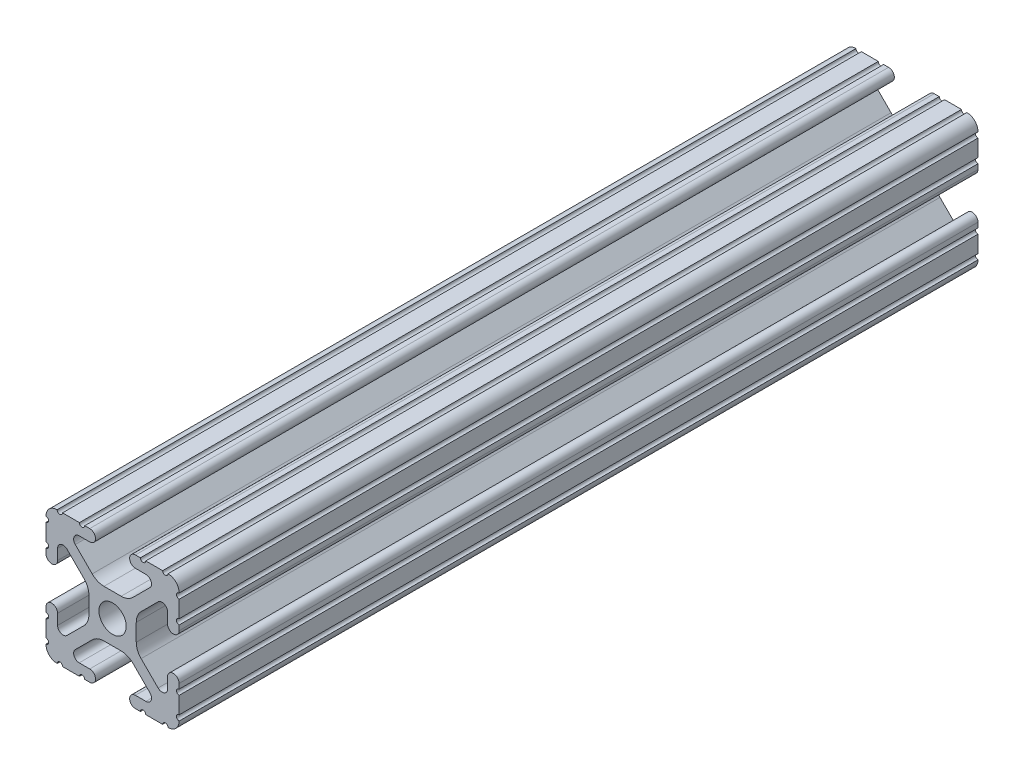
SolidWorks part; units mm, degrees
ref_plane "Front Plane" through (0, 0, 0) normal (0, 0, 1) x (1, 0, 0)
ref_plane "Top Plane" through (0, 0, 0) normal (0, 1, 0) x (1, 0, 0)
ref_plane "Right Plane" through (0, 0, 0) normal (1, 0, 0) x (0, 0, -1)
sketch "Sketch1" plane through (0, 0, 0) normal (1, 0, 0) x (0, 0, -1)
  line L0 (-76.2, 0) -> (76.2, 0)
  point P2 (0, 0)
  dimension "D1" = 152.4
other "Fractional 1010(1)"
ref_plane "Plane1" through (0, 0, 76.2) normal (0, 0, -1) x (0, 1, 0)
sketch "Sketch11" plane through (0, 0, 76.2) normal (0, 0, -1) x (0, 1, 0)
  line L0 (10.5918, 12.7) -> (10.5664, 12.7)
  line L1 (9.5504, 12.7) -> (6.3246, 12.7)
  line L2 (5.3086, 12.7) -> (4.3561, 12.7)
  line L3 (4.3561, 10.4902) -> (6.3701, 10.4902)
  line L4 (7.1192, 8.6817) -> (3.8846, 5.4471)
  line L5 (1.6396, 4.5172) -> (-1.6396, 4.5172)
  line L6 (-3.8846, 5.4471) -> (-7.1192, 8.6817)
  line L7 (-6.3701, 10.4902) -> (-4.3561, 10.4902)
  line L8 (-4.3561, 12.7) -> (-5.3086, 12.7)
  line L9 (-6.3246, 12.7) -> (-9.5504, 12.7)
  line L10 (-10.5664, 12.7) -> (-10.5918, 12.7)
  line L11 (-12.7, 10.5918) -> (-12.7, 10.5664)
  line L12 (-12.7, 9.5504) -> (-12.7, 6.3246)
  line L13 (-12.7, 5.3086) -> (-12.7, 4.3561)
  line L14 (-10.4902, 4.3561) -> (-10.4902, 6.3701)
  line L15 (-8.6817, 7.1192) -> (-5.4471, 3.8846)
  line L16 (-4.5172, 1.6396) -> (-4.5172, -1.6396)
  line L17 (-5.4471, -3.8846) -> (-8.6817, -7.1192)
  line L18 (-10.4902, -6.3701) -> (-10.4902, -4.3561)
  line L19 (-12.7, -4.3561) -> (-12.7, -5.3086)
  line L20 (-12.7, -6.3246) -> (-12.7, -9.5504)
  line L21 (-12.7, -10.5664) -> (-12.7, -10.5918)
  line L22 (-10.5918, -12.7) -> (-10.5664, -12.7)
  line L23 (-9.5504, -12.7) -> (-6.3246, -12.7)
  line L24 (-5.3086, -12.7) -> (-4.3561, -12.7)
  line L25 (-4.3561, -10.4902) -> (-6.3701, -10.4902)
  line L26 (-7.1192, -8.6817) -> (-3.8846, -5.4471)
  line L27 (-1.6396, -4.5172) -> (1.6396, -4.5172)
  line L28 (3.8846, -5.4471) -> (7.1192, -8.6817)
  line L29 (6.3701, -10.4902) -> (4.3561, -10.4902)
  line L30 (4.3561, -12.7) -> (5.3086, -12.7)
  line L31 (6.3246, -12.7) -> (9.5504, -12.7)
  line L32 (10.5664, -12.7) -> (10.5918, -12.7)
  line L33 (12.7, -10.5918) -> (12.7, -10.5664)
  line L34 (12.7, -9.5504) -> (12.7, -6.3246)
  line L35 (12.7, -5.3086) -> (12.7, -4.3561)
  line L36 (10.4902, -4.3561) -> (10.4902, -6.3701)
  line L37 (8.6817, -7.1192) -> (5.4471, -3.8846)
  line L38 (4.5172, -1.6396) -> (4.5172, 1.6396)
  line L39 (5.4471, 3.8846) -> (8.6817, 7.1192)
  line L40 (10.4902, 6.3701) -> (10.4902, 4.3561)
  line L41 (12.7, 4.3561) -> (12.7, 5.3086)
  line L42 (12.7, 6.3246) -> (12.7, 9.5504)
  line L43 (12.7, 10.5664) -> (12.7, 10.5918)
  circle A0 centre (0, 0) radius 2.6035
  arc A1 (12.7, 10.5918) -> (10.5918, 12.7) centre (10.5918, 10.5918) ccw
  arc A2 (9.5504, 12.7) -> (10.5664, 12.7) centre (10.0584, 12.7) ccw
  arc A3 (5.3086, 12.7) -> (6.3246, 12.7) centre (5.8166, 12.7) ccw
  arc A4 (4.3561, 12.7) -> (4.3561, 10.4902) centre (4.3561, 11.5951) ccw
  arc A5 (7.1192, 8.6817) -> (6.3701, 10.4902) centre (6.3701, 9.4308) ccw
  arc A6 (1.6396, 4.5172) -> (3.8846, 5.4471) centre (1.6396, 7.6922) ccw
  arc A7 (-3.8846, 5.4471) -> (-1.6396, 4.5172) centre (-1.6396, 7.6922) ccw
  arc A8 (-6.3701, 10.4902) -> (-7.1192, 8.6817) centre (-6.3701, 9.4308) ccw
  arc A9 (-4.3561, 10.4902) -> (-4.3561, 12.7) centre (-4.3561, 11.5951) ccw
  arc A10 (-6.3246, 12.7) -> (-5.3086, 12.7) centre (-5.8166, 12.7) ccw
  arc A11 (-10.5664, 12.7) -> (-9.5504, 12.7) centre (-10.0584, 12.7) ccw
  arc A12 (-10.5918, 12.7) -> (-12.7, 10.5918) centre (-10.5918, 10.5918) ccw
  arc A13 (-12.7, 9.5504) -> (-12.7, 10.5664) centre (-12.7, 10.0584) ccw
  arc A14 (-12.7, 5.3086) -> (-12.7, 6.3246) centre (-12.7, 5.8166) ccw
  arc A15 (-12.7, 4.3561) -> (-10.4902, 4.3561) centre (-11.5951, 4.3561) ccw
  arc A16 (-8.6817, 7.1192) -> (-10.4902, 6.3701) centre (-9.4308, 6.3701) ccw
  arc A17 (-4.5172, 1.6396) -> (-5.4471, 3.8846) centre (-7.6922, 1.6396) ccw
  arc A18 (-5.4471, -3.8846) -> (-4.5172, -1.6396) centre (-7.6922, -1.6396) ccw
  arc A19 (-10.4902, -6.3701) -> (-8.6817, -7.1192) centre (-9.4308, -6.3701) ccw
  arc A20 (-10.4902, -4.3561) -> (-12.7, -4.3561) centre (-11.5951, -4.3561) ccw
  arc A21 (-12.7, -6.3246) -> (-12.7, -5.3086) centre (-12.7, -5.8166) ccw
  arc A22 (-12.7, -10.5664) -> (-12.7, -9.5504) centre (-12.7, -10.0584) ccw
  arc A23 (-12.7, -10.5918) -> (-10.5918, -12.7) centre (-10.5918, -10.5918) ccw
  arc A24 (-9.5504, -12.7) -> (-10.5664, -12.7) centre (-10.0584, -12.7) ccw
  arc A25 (-5.3086, -12.7) -> (-6.3246, -12.7) centre (-5.8166, -12.7) ccw
  arc A26 (-4.3561, -12.7) -> (-4.3561, -10.4902) centre (-4.3561, -11.5951) ccw
  arc A27 (-7.1192, -8.6817) -> (-6.3701, -10.4902) centre (-6.3701, -9.4308) ccw
  arc A28 (-1.6396, -4.5172) -> (-3.8846, -5.4471) centre (-1.6396, -7.6922) ccw
  arc A29 (3.8846, -5.4471) -> (1.6396, -4.5172) centre (1.6396, -7.6922) ccw
  arc A30 (6.3701, -10.4902) -> (7.1192, -8.6817) centre (6.3701, -9.4308) ccw
  arc A31 (4.3561, -10.4902) -> (4.3561, -12.7) centre (4.3561, -11.5951) ccw
  arc A32 (6.3246, -12.7) -> (5.3086, -12.7) centre (5.8166, -12.7) ccw
  arc A33 (10.5664, -12.7) -> (9.5504, -12.7) centre (10.0584, -12.7) ccw
  arc A34 (10.5918, -12.7) -> (12.7, -10.5918) centre (10.5918, -10.5918) ccw
  arc A35 (12.7, -9.5504) -> (12.7, -10.5664) centre (12.7, -10.0584) ccw
  arc A36 (12.7, -5.3086) -> (12.7, -6.3246) centre (12.7, -5.8166) ccw
  arc A37 (12.7, -4.3561) -> (10.4902, -4.3561) centre (11.5951, -4.3561) ccw
  arc A38 (8.6817, -7.1192) -> (10.4902, -6.3701) centre (9.4308, -6.3701) ccw
  arc A39 (4.5172, -1.6396) -> (5.4471, -3.8846) centre (7.6922, -1.6396) ccw
  arc A40 (5.4471, 3.8846) -> (4.5172, 1.6396) centre (7.6922, 1.6396) ccw
  arc A41 (10.4902, 6.3701) -> (8.6817, 7.1192) centre (9.4308, 6.3701) ccw
  arc A42 (10.4902, 4.3561) -> (12.7, 4.3561) centre (11.5951, 4.3561) ccw
  arc A43 (12.7, 6.3246) -> (12.7, 5.3086) centre (12.7, 5.8166) ccw
  arc A44 (12.7, 10.5664) -> (12.7, 9.5504) centre (12.7, 10.0584) ccw
  point P0 (0, 0)
